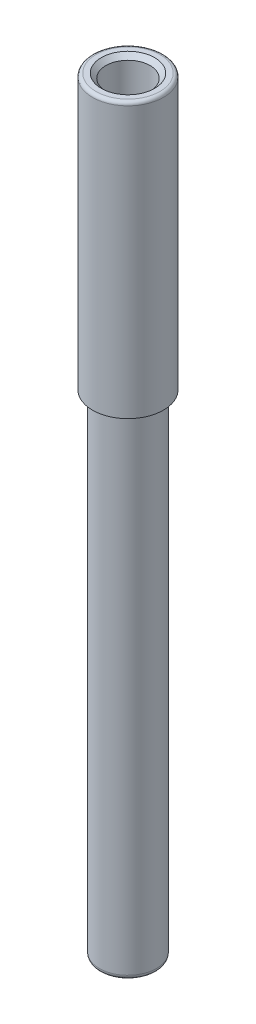
SolidWorks part; units mm, degrees
material "6061-T6 (SS)"
ref_plane "Front Plane" through (0, 0, 0) normal (0, 0, 1) x (1, 0, 0)
ref_plane "Top Plane" through (0, 0, 0) normal (0, 1, 0) x (1, 0, 0)
ref_plane "Right Plane" through (0, 0, 0) normal (1, 0, 0) x (0, 0, -1)
sketch "Sketch1" plane through (0, 0, 0) normal (0, 1, 0) x (1, 0, 0)
  circle A1 centre (0, 0) radius 3.175
  dimension "D1" = 6.35
extrude "Boss-Extrude1" add sketch "Sketch1" along normal blind 57.15
sketch "Sketch2" plane through (0, 57.15, 0) normal (0, 1, 0) x (1, 0, 0)
  point P0 (0, 0)
hole_wizard "#10 (0.1935) Diameter Hole1" positions "3DSketch1" profile "Sketch4" hole size "#10" standard "ANSI Inch"
sketch3d "3DSketch1"
  point P0 (0, 57.15, 0)
sketch "Sketch4" plane through (0, 57.15, 0) normal (1, 0, 0) x (0, 0, 1)
  line L0 (0, 0) -> (0, 56.0866)
  line L1 (0, 56.0866) -> (2.4574, 54.61)
  line L2 (2.4574, 54.61) -> (2.4574, 0)
  line L5 (2.4574, 0) -> (0, 0)
  line L10 (0, 56.0866) -> (-2.4575, 54.61) construction
  line L11 (0, -6.35) -> (0, 107.95) construction
  dimension "Hole Dia." = 4.9149
  dimension "Hole Depth" = 54.61
  dimension "Drill Angle" = 118
sketch "Sketch5" plane through (0, 57.15, 0) normal (0, 1, 0) x (1, 0, 0)
  circle A1 centre (0, 0) radius 3.175 construction
  circle A2 centre (0, 0) radius 3.937
  circle A3 centre (0, 0) radius 3.937
  circle A4 centre (0, 0) radius 3.175
  dimension "D1" = 0.762
extrude "Boss-Extrude2" add sketch "Sketch5" against normal blind 2.54
fillet "Fillet1" radius 0.508 1 edges at (0, 0, 3.175)
sketch "Sketch6" plane through (0, 57.15, 0) normal (0, 1, 0) x (1, 0, 0)
  circle A0 centre (0, 0) radius 3.937 construction
  circle A1 centre (0, 0) radius 2.4574 construction
  circle A2 centre (0, 0) radius 3.937
  circle A3 centre (0, 0) radius 2.4574
extrude "Boss-Extrude3" add sketch "Sketch6" along normal blind 27.94
chamfer "Chamfer1" distance 0.508 angle 45 1 edges at (0, 85.09, 2.4574)
fillet "Fillet2" radius 0.381 1 edges at (0, 85.09, 3.937)
ref_plane "Plane1" through (0, 84.582, 0) normal (0, -1, 0) x (-1, 0, 0)
other "Intersect1" [suppressed]
